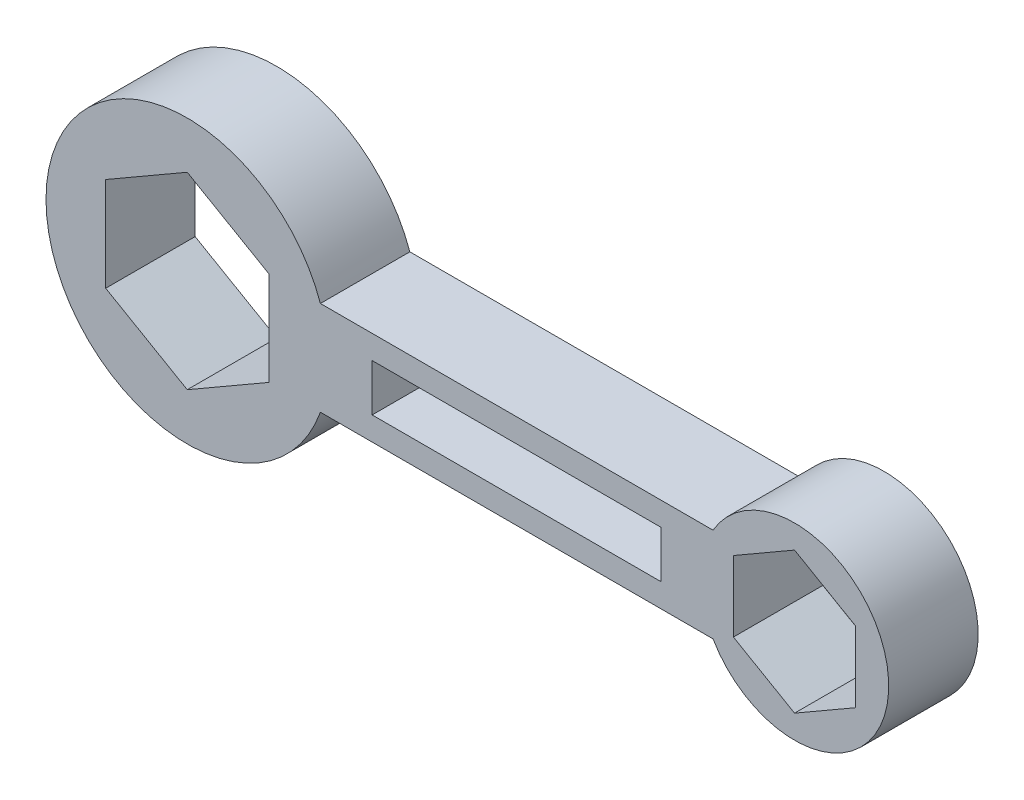
SolidWorks part; units mm, degrees
ref_plane "Front Plane" through (0, 0, 0) normal (0, 0, 1) x (1, 0, 0)
ref_plane "Top Plane" through (0, 0, 0) normal (0, 1, 0) x (1, 0, 0)
ref_plane "Right Plane" through (0, 0, 0) normal (1, 0, 0) x (0, 0, -1)
sketch "Sketch1" plane through (0, 0, 0) normal (0, 0, 1) x (1, 0, 0)
  line L10 (38.3504, -6.3131) -> (-45.0448, -6.3131)
  line L16 (38.3504, -26.3131) -> (-45.0448, -26.3131)
  circle A0 centre (-73.3291, -16.3131) radius 30
  circle A2 centre (55.6709, -16.3131) radius 20
  dimension "D3" = 60
  dimension "D6" = 40
  dimension "D9" = 129
extrude "Boss-Extrude4" add sketch "Sketch1" along normal blind 19
sketch "Sketch3" plane through (0, 0, 19) normal (0, 0, 1) x (1, 0, 0)
  line L6 (-73.3291, 3.6869) -> (-90.6496, -6.3131)
  line L7 (-90.6496, -6.3131) -> (-90.6496, -26.3131)
  line L8 (-90.6496, -26.3131) -> (-73.3291, -36.3131)
  line L9 (-73.3291, -36.3131) -> (-56.0086, -26.3131)
  line L10 (-56.0086, -26.3131) -> (-56.0086, -6.3131)
  line L11 (-56.0086, -6.3131) -> (-73.3291, 3.6869)
  line L12 (55.6709, -1.3131) -> (42.6805, -8.8131)
  line L13 (42.6805, -8.8131) -> (42.6805, -23.8131)
  line L14 (42.6805, -23.8131) -> (55.6709, -31.3131)
  line L15 (55.6709, -31.3131) -> (68.6613, -23.8131)
  line L16 (68.6613, -23.8131) -> (68.6613, -8.8131)
  line L17 (68.6613, -8.8131) -> (55.6709, -1.3131)
  line L24 (-34.0448, -11.3131) -> (27.3504, -11.3131)
  line L25 (-34.0448, -11.3131) -> (-34.0448, -21.3131)
  line L26 (-34.0448, -21.3131) -> (27.3504, -21.3131)
  line L27 (27.3504, -11.3131) -> (27.3504, -21.3131)
  circle A0 centre (-73.3291, -16.3131) radius 17.3205 construction
  circle A1 centre (55.6709, -16.3131) radius 12.9904 construction
  dimension "D1" = 20
  dimension "D2" = 15
extrude "Cut-Extrude2" cut sketch "Sketch3" against normal blind 19
sketch "Sketch4" plane through (0, 0, 19) normal (0, 0, 1) x (1, 0, 0)
  line L0 (35.1511, -12.4965) -> (89.8563, -12.4965) construction
